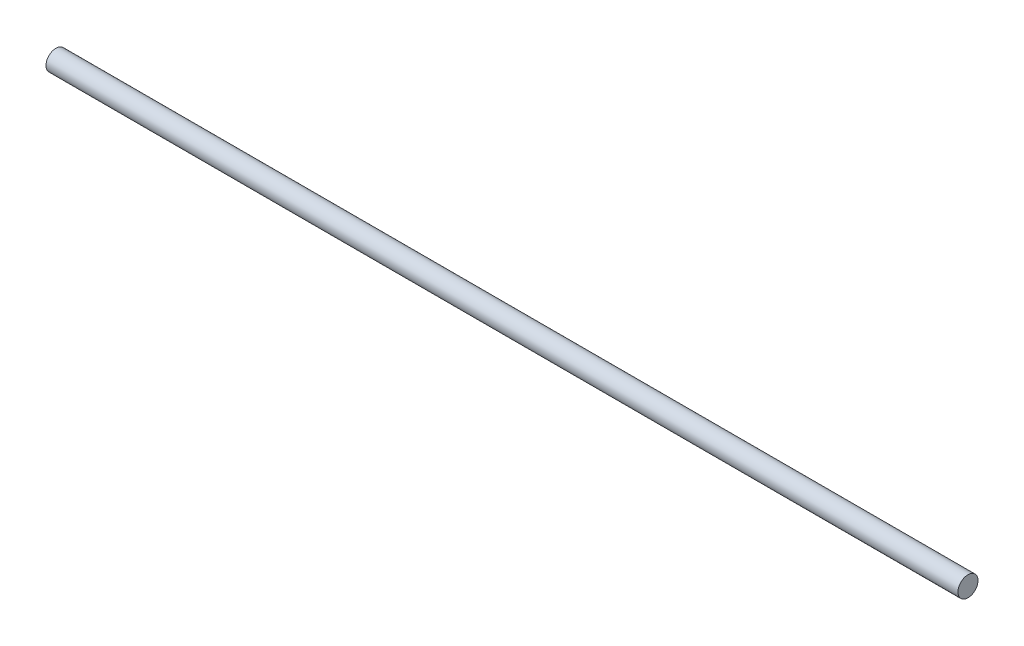
SolidWorks part; units mm, degrees
material "2018 Alloy"
ref_plane "Front Plane" through (0, 0, 0) normal (0, 0, 1) x (1, 0, 0)
ref_plane "Top Plane" through (0, 0, 0) normal (0, 1, 0) x (1, 0, 0)
ref_plane "Right Plane" through (0, 0, 0) normal (1, 0, 0) x (0, 0, -1)
sketch "Sketch1" plane through (0, 0, 0) normal (1, 0, 0) x (0, 0, -1)
  circle A0 centre (0, 0) radius 5.588
  dimension "D1" = 11.176
extrude "Boss-Extrude1" add sketch "Sketch1" along normal blind 508
sketch "Sketch2" plane through (0, 0, 0) normal (0, 0, 1) x (1, 0, 0)
  line L0 (0, 0) -> (25.4, 0) construction
  line L2 (25.4, 0) -> (508, 0) construction
  line L3 (508, -5.588) -> (508, 5.588) construction
  dimension "D1" = 25.4
